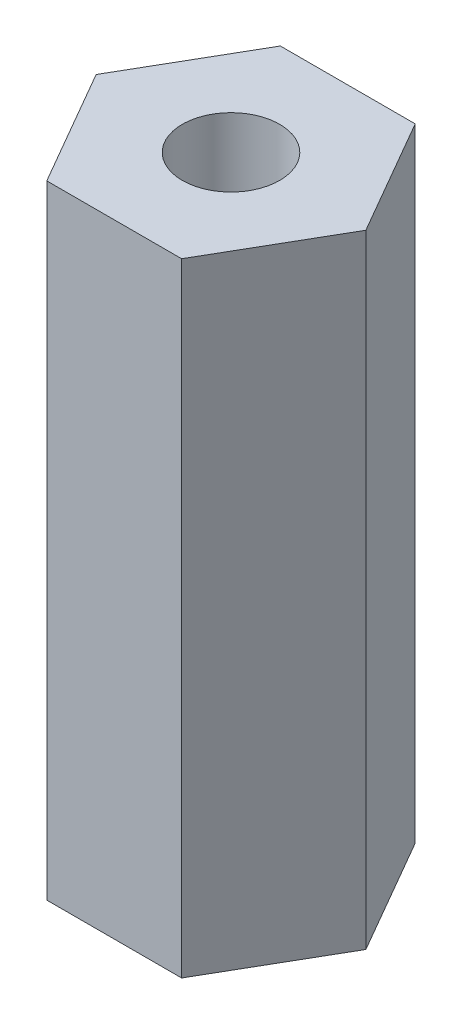
SolidWorks part; units mm, degrees
material "6061 Alloy"
ref_plane "Front Plane" through (0, 0, 0) normal (0, 0, 1) x (1, 0, 0)
ref_plane "Top Plane" through (0, 0, 0) normal (0, 1, 0) x (1, 0, 0)
ref_plane "Right Plane" through (0, 0, 0) normal (1, 0, 0) x (0, 0, -1)
sketch "Sketch1" plane through (0, 0, 0) normal (0, 1, 0) x (1, 0, 0)
  line L1 (1.7321, 3) -> (-1.7321, 3)
  line L2 (-1.7321, 3) -> (-3.4641, 0)
  line L3 (-3.4641, 0) -> (-1.7321, -3)
  line L4 (-1.7321, -3) -> (1.7321, -3)
  line L5 (1.7321, -3) -> (3.4641, 0)
  line L6 (3.4641, 0) -> (1.7321, 3)
  circle A0 centre (0, 0) radius 3 construction
  dimension "D1" = 6
extrude "Boss-Extrude1" add sketch "Sketch1" along normal blind 16
hole_wizard "M3x0.5 Tapped Hole1" positions "Sketch3" profile "Sketch4" tap size "M3x0.5" standard "Ansi Metric" end condition through all
sketch "Sketch3" plane through (0, 16, 0) normal (0, 1, 0) x (-1, 0, 0)
  point P0 (0, 0)
sketch "Sketch4" plane through (0, 16, 0) normal (1, 0, 0) x (0, 0, 1)
  line L0 (0, 0) -> (0, 16)
  line L1 (0, 16) -> (1.25, 16)
  line L2 (1.25, 16) -> (1.25, 0)
  line L5 (1.25, 0) -> (0, 0)
  line L11 (0, -6.35) -> (0, 107.95) construction
  dimension "Thru Tap Drill Dia." = 2.5
  dimension "Thru Tap Drill Depth" = 16
cosmetic thread "Hole Thread1" parameters "D2"=3
